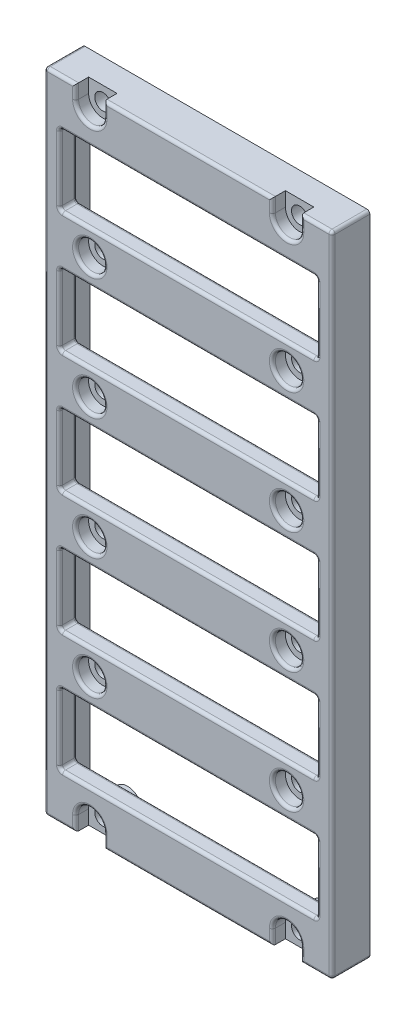
SolidWorks part; units mm, degrees
material "Nylon 101"
ref_plane "Front Plane" through (0, 0, 0) normal (0, 0, 1) x (1, 0, 0)
ref_plane "Top Plane" through (0, 0, 0) normal (0, 1, 0) x (1, 0, 0)
ref_plane "Right Plane" through (0, 0, 0) normal (1, 0, 0) x (0, 0, -1)
sketch "Sketch1" plane through (0, 0, 0) normal (0, 0, 1) x (1, 0, 0)
  line L1 (-39.37, -124.9522) -> (-63.5, -124.9522) construction
  line L2 (-15.24, -177.7842) -> (-15.24, -72.1202)
  line L4 (-63.5, -177.7842) -> (-63.5, -72.1202)
  line L5 (-15.24, -177.7842) -> (-63.5, -72.1202) construction
  line L6 (-15.24, -72.1202) -> (-63.5, -177.7842) construction
  line L8 (-15.24, -72.1202) -> (-15.24, -70.5962)
  line L9 (-15.24, -70.5962) -> (-63.5, -70.5962)
  line L10 (-15.24, -177.7842) -> (-15.24, -179.3082)
  line L11 (-15.24, -179.3082) -> (-63.5, -179.3082)
  line L12 (-63.5, -177.7842) -> (-63.5, -179.3082)
  line L13 (-15.24, -177.7842) -> (-63.5, -179.3082) construction
  line L14 (-15.24, -179.3082) -> (-63.5, -177.7842) construction
  line L15 (-63.5, -72.1202) -> (-63.5, -70.5962)
  point P4 (-39.37, -124.9522)
  point P8 (-39.37, -178.5462)
  dimension "D1" = 1.524
extrude "Boss-Extrude1" add sketch "Sketch1" along normal blind 6.35
hole_wizard "CBORE for #2 Socket Head Cap Screw1" positions "Sketch3" profile "Sketch2" counterbore size "#2" standard "ANSI Inch" end condition through all
sketch "Sketch3" plane through (0, 0, 6.35) normal (0, 0, 1) x (1, 0, 0)
  line L0 (-22.86, -179.3082) -> (-22.86, -70.5962) construction
  line L1 (-63.5, -179.3082) -> (-15.24, -179.3082) construction
  line L2 (-15.24, -70.5962) -> (-63.5, -70.5962) construction
  line L3 (-20.828, -74.1522) -> (-24.892, -74.1522) construction
  line L4 (-39.37, -179.3082) -> (-39.37, -70.5962) construction
  line L7 (-57.912, -74.1522) -> (-53.848, -74.1522) construction
  line L8 (-55.88, -179.3082) -> (-55.88, -70.5962) construction
  point P24 (-22.86, -74.1522)
  point P25 (-22.86, -72.9838)
  point P28 (-22.86, -94.4722)
  point P31 (-22.86, -114.7922)
  point P34 (-22.86, -135.1122)
  point P37 (-22.86, -155.4322)
  point P40 (-22.86, -176.9206)
  point P53 (-55.88, -176.9206)
  point P54 (-55.88, -155.4322)
  point P55 (-55.88, -135.1122)
  point P56 (-55.88, -114.7922)
  point P57 (-55.88, -94.4722)
  point P58 (-55.88, -72.9838)
  dimension "D1" = 2.3876
  dimension "D2" = 2.3876
sketch "Sketch2" plane through (-55.88, -72.9838, 6.35) normal (1, 0, 0) x (0, -1, 0)
  line L0 (0, 0) -> (0, 6.35)
  line L1 (0, 6.35) -> (1.3525, 6.35)
  line L3 (1.3525, 6.35) -> (1.3526, 2.1844)
  line L4 (1.3526, 2.1844) -> (2.3812, 2.1844)
  line L5 (2.3812, 2.1844) -> (2.3812, 0)
  line L7 (2.3812, 0) -> (0, 0)
  line L11 (0, -6.35) -> (0, 107.95) construction
  dimension "Thru Hole Dia." = 2.7051
  dimension "Thru Hole Depth" = 6.35
  dimension "C'Bore Dia." = 4.7625
  dimension "C'Bore Depth" = 2.1844
sketch "Sketch4" plane through (0, 0, 6.35) normal (0, 0, 1) x (1, 0, 0)
  line L0 (-63.5, -179.3082) -> (-15.24, -179.3082) construction
  line L1 (-20.4788, -176.9206) -> (-25.2412, -176.9206)
  line L2 (-20.4788, -176.9206) -> (-20.4788, -179.3082)
  line L3 (-20.4788, -179.3082) -> (-25.2412, -179.3082)
  line L4 (-25.2412, -176.9206) -> (-25.2412, -179.3082)
  line L5 (-20.4788, -176.9206) -> (-25.2412, -179.3082) construction
  line L6 (-20.4788, -179.3082) -> (-25.2412, -176.9206) construction
  line L7 (-22.86, -176.9206) -> (-22.86, -179.3082) construction
  line L8 (-39.37, -179.3082) -> (-39.37, -124.9522) construction
  line L9 (-39.37, -124.9522) -> (-63.5, -124.9522) construction
  line L10 (-63.5, -70.5962) -> (-63.5, -179.3082) construction
  line L11 (-58.2613, -176.9206) -> (-53.4988, -176.9206)
  line L12 (-58.2613, -176.9206) -> (-58.2613, -179.3082)
  line L13 (-58.2613, -179.3082) -> (-53.4988, -179.3082)
  line L14 (-53.4988, -176.9206) -> (-53.4988, -179.3082)
  line L15 (-20.4788, -72.9838) -> (-25.2413, -72.9838)
  line L16 (-20.4788, -72.9838) -> (-20.4788, -70.5962)
  line L17 (-20.4788, -70.5962) -> (-25.2413, -70.5962)
  line L18 (-25.2413, -72.9838) -> (-25.2413, -70.5962)
  line L19 (-53.4988, -72.9838) -> (-53.4988, -70.5962)
  line L20 (-58.2612, -70.5962) -> (-53.4988, -70.5962)
  line L21 (-58.2612, -72.9838) -> (-58.2612, -70.5962)
  line L22 (-58.2612, -72.9838) -> (-53.4988, -72.9838)
  circle A0 centre (-22.86, -176.9206) radius 2.3812 construction
  point P4 (-22.86, -178.1144)
extrude "Cut-Extrude1" cut sketch "Sketch4" against normal up to surface (2.1844 mm away) up to face at (-21.5074, -176.9206, 4.1656)
sketch "Sketch5" plane through (0, 0, 6.35) normal (0, 0, 1) x (1, 0, 0)
  line L0 (-17.78, -151.2254) -> (-60.96, -139.3191) construction
  line L1 (-17.78, -171.5454) -> (-60.96, -171.5454)
  line L2 (-17.78, -171.5454) -> (-17.78, -159.6391)
  line L3 (-17.78, -159.6391) -> (-60.96, -159.6391)
  line L4 (-60.96, -171.5454) -> (-60.96, -159.6391)
  line L5 (-17.78, -171.5454) -> (-60.96, -159.6391) construction
  line L6 (-17.78, -159.6391) -> (-60.96, -171.5454) construction
  line L7 (-17.78, -139.3191) -> (-60.96, -151.2254) construction
  line L8 (-17.78, -151.2254) -> (-17.78, -139.3191)
  line L9 (-17.78, -151.2254) -> (-60.96, -151.2254)
  line L10 (-60.96, -151.2254) -> (-60.96, -139.3191)
  line L11 (-17.78, -139.3191) -> (-60.96, -139.3191)
  line L12 (-17.78, -130.9054) -> (-60.96, -118.9991) construction
  line L13 (-17.78, -118.9991) -> (-60.96, -130.9054) construction
  line L14 (-17.78, -130.9054) -> (-17.78, -118.9991)
  line L15 (-17.78, -130.9054) -> (-60.96, -130.9054)
  line L16 (-60.96, -130.9054) -> (-60.96, -118.9991)
  line L17 (-17.78, -118.9991) -> (-60.96, -118.9991)
  line L18 (-17.78, -110.5854) -> (-60.96, -98.6791) construction
  line L19 (-17.78, -98.6791) -> (-60.96, -110.5854) construction
  line L20 (-17.78, -110.5854) -> (-17.78, -98.6791)
  line L21 (-17.78, -110.5854) -> (-60.96, -110.5854)
  line L22 (-60.96, -110.5854) -> (-60.96, -98.6791)
  line L23 (-17.78, -98.6791) -> (-60.96, -98.6791)
  line L24 (-17.78, -90.2654) -> (-60.96, -78.3591) construction
  line L25 (-17.78, -78.3591) -> (-60.96, -90.2654) construction
  line L26 (-17.78, -90.2654) -> (-17.78, -78.3591)
  line L27 (-17.78, -90.2654) -> (-60.96, -90.2654)
  line L28 (-60.96, -90.2654) -> (-60.96, -78.3591)
  line L29 (-17.78, -78.3591) -> (-60.96, -78.3591)
  point P4 (-39.37, -165.5922)
  point P13 (-39.37, -145.2722)
  point P18 (-39.37, -124.9522)
  point P23 (-39.37, -104.6322)
  point P28 (-39.37, -84.3122)
  dimension "D1" = 5
extrude "Cut-Extrude2" cut sketch "Sketch5" against normal through all
sketch "Sketch6" plane through (0, 0, 0) normal (0, 0, -1) x (-1, 0, 0)
  line L0 (20.4788, -72.9838) -> (20.4788, -70.5962) construction
  line L1 (25.2413, -70.5962) -> (25.2413, -72.9838) construction
  line L2 (53.4988, -72.9838) -> (53.4988, -70.5962) construction
  line L3 (58.2612, -70.5962) -> (58.2612, -72.9838) construction
  line L4 (20.4788, -179.3082) -> (20.4788, -176.9206) construction
  line L5 (25.2412, -176.9206) -> (25.2412, -179.3082) construction
  line L6 (53.4988, -179.3082) -> (53.4988, -176.9206) construction
  line L7 (58.2612, -176.9206) -> (58.2613, -179.3082) construction
  line L8 (20.4788, -72.9838) -> (20.4788, -71.8662)
  line L9 (25.2413, -71.8662) -> (25.2413, -72.9838)
  line L10 (53.4988, -72.9838) -> (53.4988, -71.8662)
  line L11 (58.2612, -71.8662) -> (58.2612, -72.9838)
  line L12 (20.4788, -178.0382) -> (20.4788, -176.9206)
  line L13 (25.2412, -176.9206) -> (25.2412, -178.0382)
  line L14 (53.4988, -178.0382) -> (53.4988, -176.9206)
  line L15 (58.2612, -176.9206) -> (58.2612, -178.0382)
  line L17 (62.23, -71.8662) -> (58.2612, -71.8662)
  line L18 (16.51, -71.8662) -> (16.51, -178.0382)
  line L19 (16.51, -178.0382) -> (20.4788, -178.0382)
  line L20 (15.24, -70.5962) -> (15.24, -179.3082)
  line L21 (15.24, -179.3082) -> (63.5, -179.3082)
  line L22 (63.5, -179.3082) -> (63.5, -70.5962)
  line L23 (63.5, -70.5962) -> (15.24, -70.5962)
  line L24 (15.24, -70.5962) -> (15.24, -179.3082) construction
  line L25 (15.24, -179.3082) -> (63.5, -179.3082) construction
  line L26 (63.5, -179.3082) -> (63.5, -70.5962) construction
  line L27 (63.5, -70.5962) -> (15.24, -70.5962) construction
  line L28 (62.23, -178.0382) -> (62.23, -71.8662)
  line L29 (17.78, -110.5854) -> (60.96, -110.5854)
  line L30 (17.78, -98.6791) -> (17.78, -110.5854)
  line L31 (60.96, -98.6791) -> (17.78, -98.6791)
  line L32 (60.96, -110.5854) -> (60.96, -98.6791)
  line L33 (17.78, -110.5854) -> (60.96, -110.5854)
  line L34 (17.78, -98.6791) -> (17.78, -110.5854)
  line L35 (60.96, -98.6791) -> (17.78, -98.6791)
  line L36 (60.96, -110.5854) -> (60.96, -98.6791)
  line L37 (17.78, -90.2654) -> (60.96, -90.2654)
  line L38 (17.78, -78.3591) -> (17.78, -90.2654)
  line L39 (60.96, -78.3591) -> (17.78, -78.3591)
  line L40 (60.96, -90.2654) -> (60.96, -78.3591)
  line L41 (17.78, -90.2654) -> (60.96, -90.2654)
  line L42 (17.78, -78.3591) -> (17.78, -90.2654)
  line L43 (60.96, -78.3591) -> (17.78, -78.3591)
  line L44 (60.96, -90.2654) -> (60.96, -78.3591)
  line L45 (17.78, -130.9054) -> (60.96, -130.9054)
  line L46 (17.78, -118.9991) -> (17.78, -130.9054)
  line L47 (60.96, -118.9991) -> (17.78, -118.9991)
  line L48 (60.96, -130.9054) -> (60.96, -118.9991)
  line L49 (17.78, -130.9054) -> (60.96, -130.9054)
  line L50 (17.78, -118.9991) -> (17.78, -130.9054)
  line L51 (60.96, -118.9991) -> (17.78, -118.9991)
  line L52 (60.96, -130.9054) -> (60.96, -118.9991)
  line L53 (17.78, -151.2254) -> (60.96, -151.2254)
  line L54 (17.78, -139.3191) -> (17.78, -151.2254)
  line L55 (60.96, -139.3191) -> (17.78, -139.3191)
  line L56 (60.96, -151.2254) -> (60.96, -139.3191)
  line L57 (17.78, -151.2254) -> (60.96, -151.2254)
  line L58 (17.78, -139.3191) -> (17.78, -151.2254)
  line L59 (60.96, -139.3191) -> (17.78, -139.3191)
  line L60 (60.96, -151.2254) -> (60.96, -139.3191)
  line L61 (17.78, -159.6391) -> (17.78, -171.5454)
  line L62 (60.96, -159.6391) -> (17.78, -159.6391)
  line L63 (60.96, -171.5454) -> (60.96, -159.6391)
  line L64 (17.78, -171.5454) -> (60.96, -171.5454)
  line L65 (17.78, -159.6391) -> (17.78, -171.5454)
  line L66 (60.96, -159.6391) -> (17.78, -159.6391)
  line L67 (60.96, -171.5454) -> (60.96, -159.6391)
  line L68 (17.78, -171.5454) -> (60.96, -171.5454)
  line L69 (20.4788, -71.8662) -> (16.51, -71.8662)
  line L70 (62.23, -71.8662) -> (16.51, -71.8662) construction
  line L71 (53.4988, -71.8662) -> (25.2413, -71.8662)
  line L72 (25.2412, -178.0382) -> (53.4988, -178.0382)
  line L73 (16.51, -178.0382) -> (62.23, -178.0382) construction
  line L74 (58.2612, -178.0382) -> (62.23, -178.0382)
  arc A0 (20.4788, -72.9838) -> (25.2413, -72.9838) centre (22.86, -72.9838) ccw construction
  arc A1 (53.4988, -72.9838) -> (58.2612, -72.9838) centre (55.88, -72.9838) ccw construction
  arc A2 (25.2412, -176.9206) -> (20.4788, -176.9206) centre (22.86, -176.9206) ccw construction
  arc A3 (58.2612, -176.9206) -> (53.4988, -176.9206) centre (55.88, -176.9206) ccw construction
  arc A4 (20.4788, -72.9838) -> (25.2413, -72.9838) centre (22.86, -72.9838) ccw
  arc A5 (53.4988, -72.9838) -> (58.2612, -72.9838) centre (55.88, -72.9838) ccw
  arc A6 (25.2412, -176.9206) -> (20.4788, -176.9206) centre (22.86, -176.9206) ccw
  arc A7 (58.2612, -176.9206) -> (53.4988, -176.9206) centre (55.88, -176.9206) ccw
  circle A8 centre (55.88, -155.4322) radius 2.3812 construction
  circle A9 centre (22.86, -155.4322) radius 2.3812 construction
  circle A10 centre (22.86, -135.1122) radius 2.3812 construction
  circle A11 centre (55.88, -135.1122) radius 2.3812 construction
  circle A12 centre (55.88, -114.7922) radius 2.3812 construction
  circle A13 centre (22.86, -114.7922) radius 2.3812 construction
  circle A14 centre (22.86, -94.4722) radius 2.3812 construction
  circle A15 centre (55.88, -94.4722) radius 2.3812 construction
  circle A16 centre (55.88, -155.4322) radius 2.3812
  circle A17 centre (22.86, -155.4322) radius 2.3812
  circle A18 centre (22.86, -135.1122) radius 2.3812
  circle A19 centre (55.88, -135.1122) radius 2.3812
  circle A20 centre (55.88, -114.7922) radius 2.3812
  circle A21 centre (22.86, -114.7922) radius 2.3812
  circle A22 centre (22.86, -94.4722) radius 2.3812
  circle A23 centre (55.88, -94.4722) radius 2.3812
  dimension "D1" = 0
  dimension "D2" = 0
  dimension "D3" = 0
  dimension "D4" = 0
  dimension "D5" = 0
  dimension "D6" = 0
  dimension "D7" = 1.27
extrude "Cut-Extrude3" cut sketch "Sketch6" against normal offset from surface (3.4036 mm away) 0.762 up to face at (-54.5274, -155.4322, 4.1656)
fillet "Fillet1" radius 0.508 132 edges at (-25.2413, -71.79, 6.35) (-22.86, -75.3651, 6.35) (-20.4788, -71.79, 6.35) (-17.8594, -70.5962, 6.35) (-15.24, -124.9522, 6.35) (-17.8594, -179.3082, 6.35) (-20.4788, -178.1144, 6.35) (-22.86, -174.5394, 6.35) (-25.2412, -178.1144, 6.35) (-39.37, -179.3082, 6.35) (-53.4988, -178.1144, 6.35) (-55.88, -174.5394, 6.35) (-58.2613, -178.1144, 6.35) (-60.8806, -179.3082, 6.35) (-63.5, -124.9522, 6.35) (-60.8806, -70.5962, 6.35) (-58.2612, -71.79, 6.35) (-55.88, -75.3651, 6.35) (-53.4988, -71.79, 6.35) (-39.37, -70.5962, 6.35) (-53.4988, -94.4722, 6.35) (-53.4988, -114.7922, 6.35) (-53.4988, -135.1122, 6.35) (-53.4988, -155.4322, 6.35) (-20.4788, -155.4322, 6.35) (-20.4788, -135.1122, 6.35) (-20.4788, -114.7922, 6.35) (-20.4788, -94.4722, 6.35) (-60.96, -165.5922, 6.35) (-39.37, -171.5454, 6.35) (-17.78, -165.5922, 6.35) (-39.37, -159.6391, 6.35) (-39.37, -139.3191, 6.35) (-60.96, -145.2722, 6.35) (-39.37, -151.2254, 6.35) (-17.78, -145.2722, 6.35) (-39.37, -118.9991, 6.35) (-60.96, -124.9522, 6.35) (-39.37, -130.9054, 6.35) (-17.78, -124.9522, 6.35) (-39.37, -98.6791, 6.35) (-60.96, -104.6322, 6.35) (-39.37, -110.5854, 6.35) (-17.78, -104.6322, 6.35) (-39.37, -78.3591, 6.35) (-60.96, -84.3122, 6.35) (-39.37, -90.2654, 6.35) (-17.78, -84.3122, 6.35) (-58.2612, -155.4322, 3.4036) (-25.2412, -135.1122, 3.4036) (-58.2612, -114.7922, 3.4036) (-25.2412, -94.4722, 3.4036) (-17.78, -104.6322, 3.4036) (-39.37, -110.5854, 3.4036) (-60.96, -104.6322, 3.4036) (-39.37, -98.6791, 3.4036) (-17.78, -84.3122, 3.4036) (-39.37, -90.2654, 3.4036) (-60.96, -84.3122, 3.4036) (-39.37, -78.3591, 3.4036) (-17.78, -124.9522, 3.4036) (-39.37, -130.9054, 3.4036) (-60.96, -124.9522, 3.4036) (-39.37, -118.9991, 3.4036) (-17.78, -145.2722, 3.4036) (-39.37, -151.2254, 3.4036) (-60.96, -145.2722, 3.4036) (-39.37, -139.3191, 3.4036) (-39.37, -159.6391, 3.4036) (-17.78, -165.5922, 3.4036) (-39.37, -171.5454, 3.4036) (-60.96, -165.5922, 3.4036) (-58.2613, -94.4722, 3.4036) (-25.2412, -114.7922, 3.4036) (-58.2612, -135.1122, 3.4036) (-25.2412, -155.4322, 3.4036) (-25.2413, -72.425, 3.4036) (-39.37, -71.8662, 3.4036) (-53.4988, -72.425, 3.4036) (-55.88, -75.3651, 3.4036) (-58.2612, -72.425, 3.4036) (-60.2456, -71.8662, 3.4036) (-62.23, -124.9522, 3.4036) (-60.2456, -178.0382, 3.4036) (-58.2612, -177.4794, 3.4036) (-55.88, -174.5394, 3.4036) (-53.4988, -177.4794, 3.4036) (-39.37, -178.0382, 3.4036) (-25.2412, -177.4794, 3.4036) (-22.86, -174.5394, 3.4036) (-20.4788, -177.4794, 3.4036) (-18.4944, -178.0382, 3.4036) (-16.51, -124.9522, 3.4036) (-18.4944, -71.8662, 3.4036) (-20.4788, -72.425, 3.4036) (-22.86, -75.3651, 3.4036) (-15.24, -70.5962, 3.175) (-63.5, -70.5962, 3.175) (-63.5, -179.3082, 3.175) (-15.24, -179.3082, 3.175) (-20.4788, -71.8662, 1.7018) (-16.51, -178.0382, 1.7018) (-20.4788, -178.0382, 1.7018) (-25.2412, -178.0382, 1.7018) (-53.4988, -178.0382, 1.7018) (-58.2612, -178.0382, 1.7018) (-62.23, -178.0382, 1.7018) (-62.23, -71.8662, 1.7018) (-58.2612, -71.8662, 1.7018) (-53.4988, -71.8662, 1.7018) (-25.2413, -71.8662, 1.7018) (-16.51, -71.8662, 1.7018) (-17.78, -98.6791, 4.8768) (-17.78, -110.5854, 4.8768) (-60.96, -110.5854, 4.8768) (-60.96, -98.6791, 4.8768) (-17.78, -78.3591, 4.8768) (-17.78, -90.2654, 4.8768) (-60.96, -90.2654, 4.8768) (-60.96, -78.3591, 4.8768) (-17.78, -118.9991, 4.8768) (-17.78, -130.9054, 4.8768) (-60.96, -130.9054, 4.8768) (-60.96, -118.9991, 4.8768) (-17.78, -151.2254, 4.8768) (-60.96, -151.2254, 4.8768) (-60.96, -139.3191, 4.8768) (-17.78, -139.3191, 4.8768) (-60.96, -159.6391, 4.8768) (-17.78, -171.5454, 4.8768) (-60.96, -171.5454, 4.8768) (-17.78, -159.6391, 4.8768)
sketch "Sketch7" plane through (0, 0, 0) normal (0, 0, -1) x (-1, 0, 0)
  line L1 (59.5078, -161.9188) -> (19.5816, -161.9188)
  line L2 (59.5078, -161.9188) -> (59.5078, -88.1954)
  line L3 (59.5078, -88.1954) -> (19.5816, -88.1954)
  line L4 (19.5816, -161.9188) -> (19.5816, -88.1954)
  line L5 (59.5078, -161.9188) -> (19.5816, -88.1954) construction
  line L6 (59.5078, -88.1954) -> (19.5816, -161.9188) construction
  point P4 (39.5447, -125.0571)
extrude "Cut-Extrude4" cut sketch "Sketch7" against normal blind 2.54
